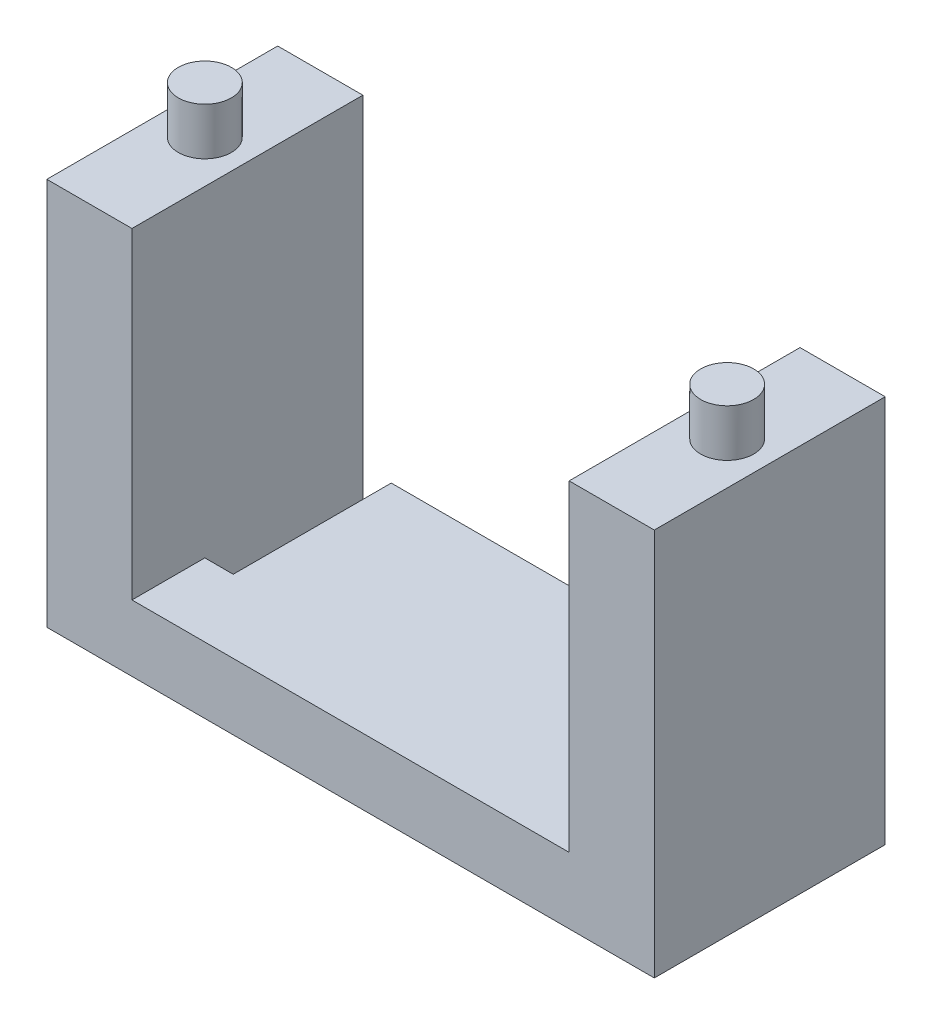
SolidWorks part; units mm, degrees
ref_plane "前视基准面" through (0, 0, 0) normal (0, 0, 1) x (1, 0, 0)
ref_plane "上视基准面" through (0, 0, 0) normal (0, 1, 0) x (1, 0, 0)
ref_plane "右视基准面" through (0, 0, 0) normal (1, 0, 0) x (0, 0, -1)
sketch "草图4" plane through (0, 0, 0) normal (0, 0, 1) x (1, 0, 0)
  line L0 (-11.55, 0) -> (11.55, 0)
  line L1 (11.55, 0) -> (11.55, 17)
  line L2 (16.05, -4.5) -> (16.05, 17)
  line L3 (0, 0) -> (0, 28356.0318) construction
  line L4 (-16.05, -4.5) -> (16.05, -4.5)
  line L5 (-11.55, 0) -> (-11.55, 17)
  line L6 (-16.05, -4.5) -> (-16.05, 17)
  line L7 (11.55, 17) -> (16.05, 17)
  line L8 (-11.55, 17) -> (-16.05, 17)
  point P10 (0, 0)
  dimension "D1" = 23.1
  dimension "D2" = 17
  dimension "D3" = 4.5
extrude "凸台-拉伸2" add sketch "草图4" along normal blind 12.2
sketch "草图5" plane through (0, -4.5, 0) normal (0, -1, 0) x (1, 0, 0)
  line L0 (-11.55, 12.2) -> (-11.55, 0) construction
  line L9 (-16.05, 0) -> (16.05, 0) construction
  line L10 (-11.55, 8.35) -> (-10.05, 8.35)
  line L11 (-11.55, 8.35) -> (-11.55, 0)
  line L12 (-11.55, 0) -> (-10.05, 0)
  line L13 (-10.05, 8.35) -> (-10.05, 0)
  point P94 (-10.8, 3.05)
  dimension "D1" = 1.5
  dimension "D2" = 8.35
extrude "切除-拉伸1" cut sketch "草图5" against normal through all
ref_plane "基准面4" through (0, 17, 0) normal (0, 1, 0) x (1, 0, 0)
sketch "草图6" plane through (0, 17, 0) normal (0, 1, 0) x (1, 0, 0)
  line L0 (11.55, 0) -> (16.05, -12.2) construction
  line L1 (16.05, 0) -> (11.55, -12.2) construction
  line L2 (11.55, -12.2) -> (-11.55, -12.2) construction
  line L3 (0, -12.2) -> (0, 0) construction
  circle A0 centre (13.8, -6.1) radius 1.4
  circle A1 centre (-13.8, -6.1) radius 1.4
  dimension "D1" = 2.8
extrude "凸台-拉伸3" add sketch "草图6" along normal blind 2.5
sketch "草图7" plane through (16.05, 0, 0) normal (1, 0, 0) x (0, 0, -1)
  line L0 (0, -4.5) -> (0, 17) construction
  line L1 (-12.2, -4.5) -> (0, -4.5)
  line L2 (-12.2, -4.5) -> (-12.2, -3.5)
  line L3 (-12.2, -3.5) -> (0, -3.5)
  line L4 (0, -4.5) -> (0, -3.5)
  line L5 (-6.1, -3.5) -> (-6.1, -4.5) construction
  line L6 (-12.2, -4) -> (0, -4) construction
  point P96 (-6.1, -4)
  dimension "D1" = 1
extrude "切除-拉伸2" cut sketch "草图7" against normal up to surface (32.1 mm away) and the other way through all up to face at (-16.05, 6.25, 6.1)
